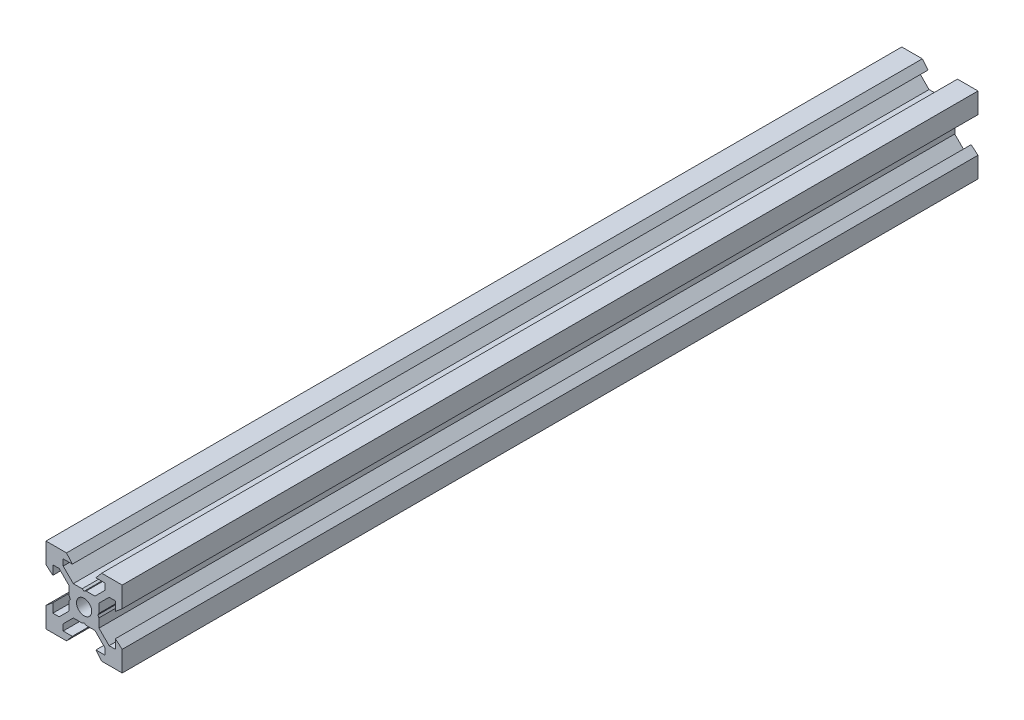
SolidWorks part; units mm, degrees
ref_plane "Front Plane" through (0, 0, 0) normal (0, 0, 1) x (1, 0, 0)
ref_plane "Top Plane" through (0, 0, 0) normal (0, 1, 0) x (1, 0, 0)
ref_plane "Right Plane" through (0, 0, 0) normal (1, 0, 0) x (0, 0, -1)
sketch "Sketch1" plane through (0, 0, 0) normal (0, 0, 1) x (1, 0, 0)
  line L0 (10, 10) -> (4.6104, 10) construction
  line L1 (10, 10) -> (10, 4.6104) construction
  line L2 (10, -10) -> (10, -4.6104) construction
  line L3 (10, -10) -> (4.6104, -10) construction
  line L4 (10, 10) -> (10, 4.6104)
  line L5 (6.5607, 5.5) -> (8.2, 5.5)
  line L6 (5.5, 8.2) -> (5.5, 6.5607)
  line L7 (10, 10) -> (4.6104, 10)
  line L8 (10, 10) -> (10, 4.6104)
  line L9 (6.5607, 5.5) -> (3.9, 2.8393)
  line L10 (5.5, 6.5607) -> (2.8393, 3.9)
  line L11 (10, 4.6104) -> (8.2, 3.1)
  line L12 (4.6104, 10) -> (3.1, 8.2)
  line L13 (8.2, 3.1) -> (8.2, 5.5)
  line L14 (3.1, 8.2) -> (5.5, 8.2)
  line L15 (-6.5607, 5.5) -> (-8.2, 5.5)
  line L16 (6.5607, -5.5) -> (8.2, -5.5)
  line L17 (3.1, -8.2) -> (5.5, -8.2)
  line L18 (8.2, -3.1) -> (8.2, -5.5)
  line L19 (4.6104, -10) -> (3.1, -8.2)
  line L20 (10, -4.6104) -> (8.2, -3.1)
  line L21 (0.5196, -3.9) -> (0, -3.6)
  line L22 (0.5196, 3.9) -> (0, 3.6)
  line L23 (3.6, 0) -> (3.9, -0.5196)
  line L24 (3.9, 0.5196) -> (3.6, 0)
  line L25 (3.9, 0.5196) -> (3.9, 2.8393)
  line L26 (2.8393, 3.9) -> (0.5196, 3.9)
  line L27 (3.9, -2.8393) -> (3.9, -0.5196)
  line L28 (2.8393, -3.9) -> (0.5196, -3.9)
  line L29 (5.5, -6.5607) -> (2.8393, -3.9)
  line L30 (6.5607, -5.5) -> (3.9, -2.8393)
  line L31 (10, -10) -> (10, -4.6104)
  line L32 (10, -10) -> (4.6104, -10)
  line L33 (5.5, -8.2) -> (5.5, -6.5607)
  line L34 (-6.5607, -5.5) -> (-8.2, -5.5)
  line L35 (10, -10) -> (10, -4.6104)
  line L36 (0, 0) -> (0, 8.2) construction
  line L37 (-10, -10) -> (-4.6104, -10) construction
  line L38 (-10, -10) -> (-10, -4.6104) construction
  line L39 (-10, 10) -> (-10, 4.6104) construction
  line L40 (-10, 10) -> (-4.6104, 10) construction
  line L41 (-10, -10) -> (-10, -4.6104)
  line L43 (-5.5, -8.2) -> (-5.5, -6.5607)
  line L44 (-10, -10) -> (-4.6104, -10)
  line L45 (-10, -10) -> (-10, -4.6104)
  line L46 (-6.5607, -5.5) -> (-3.9, -2.8393)
  line L47 (-5.5, -6.5607) -> (-2.8393, -3.9)
  line L48 (-2.8393, -3.9) -> (-0.5196, -3.9)
  line L49 (-3.9, -2.8393) -> (-3.9, -0.5196)
  line L50 (-2.8393, 3.9) -> (-0.5196, 3.9)
  line L51 (-3.9, 0.5196) -> (-3.9, 2.8393)
  line L52 (-3.9, 0.5196) -> (-3.6, 0)
  line L53 (-3.6, 0) -> (-3.9, -0.5196)
  line L54 (-0.5196, 3.9) -> (0, 3.6)
  line L55 (-0.5196, -3.9) -> (0, -3.6)
  line L56 (-10, -4.6104) -> (-8.2, -3.1)
  line L57 (-4.6104, -10) -> (-3.1, -8.2)
  line L58 (-8.2, -3.1) -> (-8.2, -5.5)
  line L59 (-3.1, -8.2) -> (-5.5, -8.2)
  line L60 (-10, -10) -> (10, -10) construction
  line L61 (-10, -10) -> (-10, 10) construction
  line L62 (-3.1, 8.2) -> (-5.5, 8.2)
  line L63 (-8.2, 3.1) -> (-8.2, 5.5)
  line L64 (-4.6104, 10) -> (-3.1, 8.2)
  line L65 (-10, 4.6104) -> (-8.2, 3.1)
  line L66 (-5.5, 6.5607) -> (-2.8393, 3.9)
  line L67 (-6.5607, 5.5) -> (-3.9, 2.8393)
  line L68 (-10, 10) -> (-10, 4.6104)
  line L69 (-10, 10) -> (-4.6104, 10)
  line L70 (-5.5, 8.2) -> (-5.5, 6.5607)
  line L71 (-10, 10) -> (10, 10) construction
  line L72 (-10, 10) -> (-10, 4.6104)
  line L73 (10, -10) -> (10, 10) construction
  line L74 (-10, -10) -> (10, 10) construction
  line L75 (-10, 10) -> (10, -10) construction
  circle A0 centre (0, 0) radius 2
  dimension "D7" = 4
  dimension "D1" = 20
  dimension "D2" = 5.3896
  dimension "D3" = 4.5
  dimension "D4" = 50
  dimension "D5" = 1.8
  dimension "D6" = 1.5104
  dimension "D8" = 5.5
  dimension "D9" = 120
  dimension "D10" = 0.3
  dimension "D11" = 2.3197
  dimension "D12" = 7.8
  dimension "D13" = 7.8
  dimension "D14" = 1.5
  dimension "D15" = 2.6607
extrude "Boss-Extrude1" add sketch "Sketch1" along normal mid plane 224.57 contours L70 L62 L64 L69 L68 L65 L63 L15 L67 L51 L52 L53 L49 L46 L34 L58 L56 L41 L44 L57 L59 L43 L47 L48 L55 L21 L28 L29 L33 L17 L19 L32 L31 L20 L18 L16 L30 L27 L23 L24 L25 L9 L5 L13 L11 L4 L7 L12 L14 L6 L10
